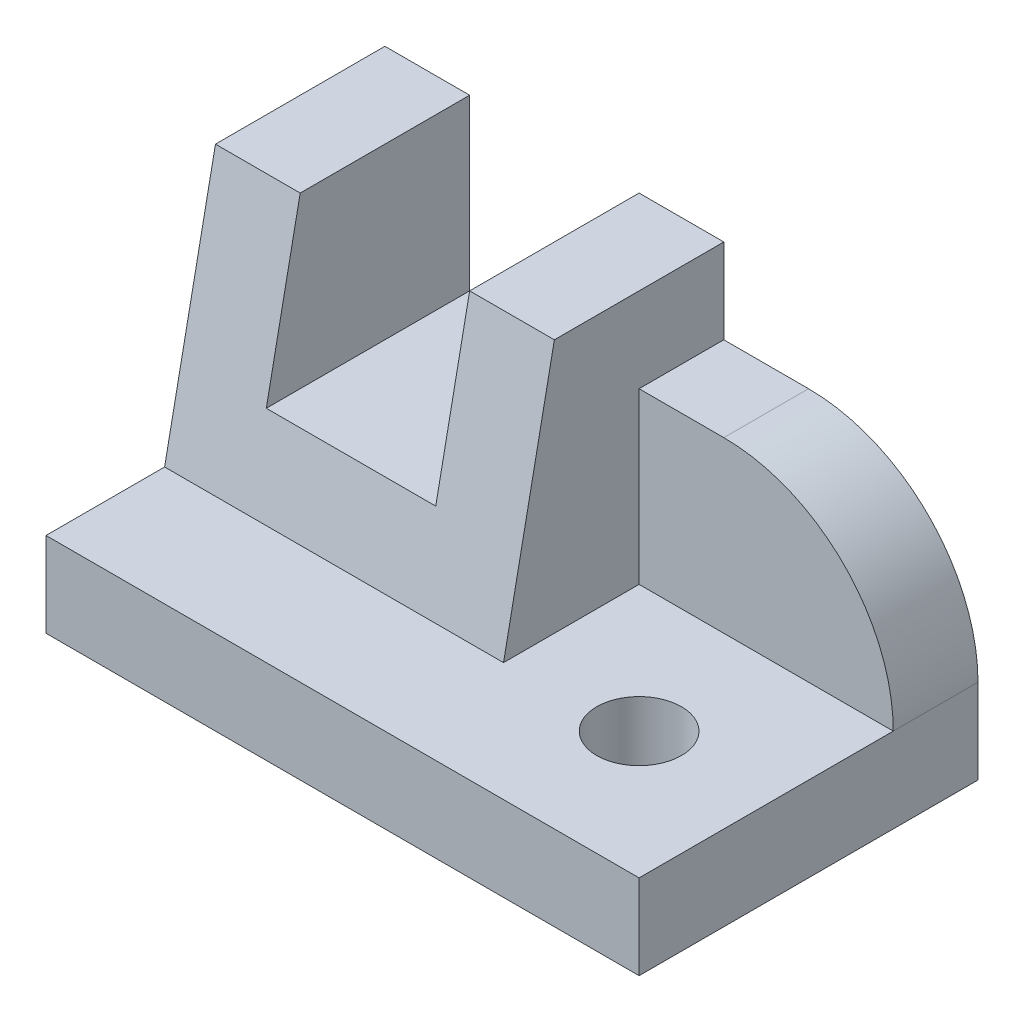
SolidWorks part; units mm, degrees
ref_plane "Front Plane" through (0, 0, 0) normal (0, 0, 1) x (1, 0, 0)
ref_plane "Top Plane" through (0, 0, 0) normal (0, 1, 0) x (1, 0, 0)
ref_plane "Right Plane" through (0, 0, 0) normal (1, 0, 0) x (0, 0, -1)
ref_plane "Plane1" through (0, 0, 0) normal (-1, 0, 0) x (0, -1, 0)
sketch "Sketch1" plane through (0, 0, 0) normal (-1, 0, 0) x (0, -1, 0)
  line L0 (-10, -14) -> (-40, -20)
  line L1 (-40, -20) -> (-10, -20)
  line L2 (-10, -20) -> (-10, -14)
  dimension "D1" = 30
  dimension "Width" = 6
extrude "Boss-Extrude1" add sketch "Sketch1" against normal blind 40
sketch "Sketch2" plane through (0, 0, -20) normal (0, 0, -1) x (-1, 0, 0)
  line L0 (-40, 40) -> (0, 40)
  line L1 (0, 40) -> (0, 10)
  line L2 (0, 10) -> (-40, 10)
  line L3 (-40, 10) -> (-40, 40)
extrude "Boss-Extrude2" add sketch "Sketch2" along normal blind 20
sketch "Sketch3" plane through (40, 0, 0) normal (1, 0, 0) x (0, 0, -1)
  line L0 (40, 10) -> (0, 10)
  line L1 (0, 10) -> (20, 40)
  line L2 (20, 40) -> (40, 40)
  line L3 (40, 40) -> (40, 10)
extrude "Boss-Extrude3" add sketch "Sketch3" along normal blind 30
sketch "Sketch4" plane through (70, 0, 0) normal (1, 0, 0) x (0, 0, -1)
  line L0 (20, 40) -> (0, 10)
  line L1 (0, 10) -> (30, 10)
  line L2 (30, 10) -> (30, 30)
  line L3 (30, 30) -> (40, 30)
  line L4 (40, 30) -> (40, 40)
  line L5 (40, 40) -> (20, 40)
extrude "Cut-Extrude1" cut sketch "Sketch4" against normal blind 30
sketch "Sketch5" plane through (0, 10, 0) normal (0, -1, 0) x (1, 0, 0)
  line L0 (70, 0) -> (70, -40)
  line L1 (70, -40) -> (0, -40)
  line L2 (0, -40) -> (0, 0)
  line L3 (0, 0) -> (70, 0)
extrude "Boss-Extrude4" add sketch "Sketch5" along normal blind 10
sketch "Sketch6" plane through (0, 0, -40) normal (0, 0, -1) x (-1, 0, 0)
  line L0 (-30, 40) -> (-30, 20)
  line L1 (-30, 20) -> (-10, 20)
  line L2 (-10, 20) -> (-10, 40)
  line L3 (-10, 40) -> (-30, 40)
extrude "Cut-Extrude2" cut sketch "Sketch6" against normal through all
hole_wizard "Ø10.0 (10) Diameter Hole1" positions "Sketch8" profile "Sketch7" hole size "Ø10.0" standard "ANSI Metric"
sketch "Sketch8" plane through (0, 0, 0) normal (0, -1, 0) x (-1, 0, 0)
  point P0 (-55, 15)
sketch "Sketch7" plane through (55, 0, -15) normal (1, 0, 0) x (0, 0, -1)
  line L0 (0, 0) -> (0, 40)
  line L1 (0, 40) -> (5, 40)
  line L2 (5, 40) -> (5, 0)
  line L5 (5, 0) -> (0, 0)
  line L11 (0, -6.35) -> (0, 107.95) construction
  dimension "Thru Hole Dia." = 10
  dimension "Thru Hole Depth" = 40
fillet "Fillet1" radius 20 1 edges at (70, 30, -35)
